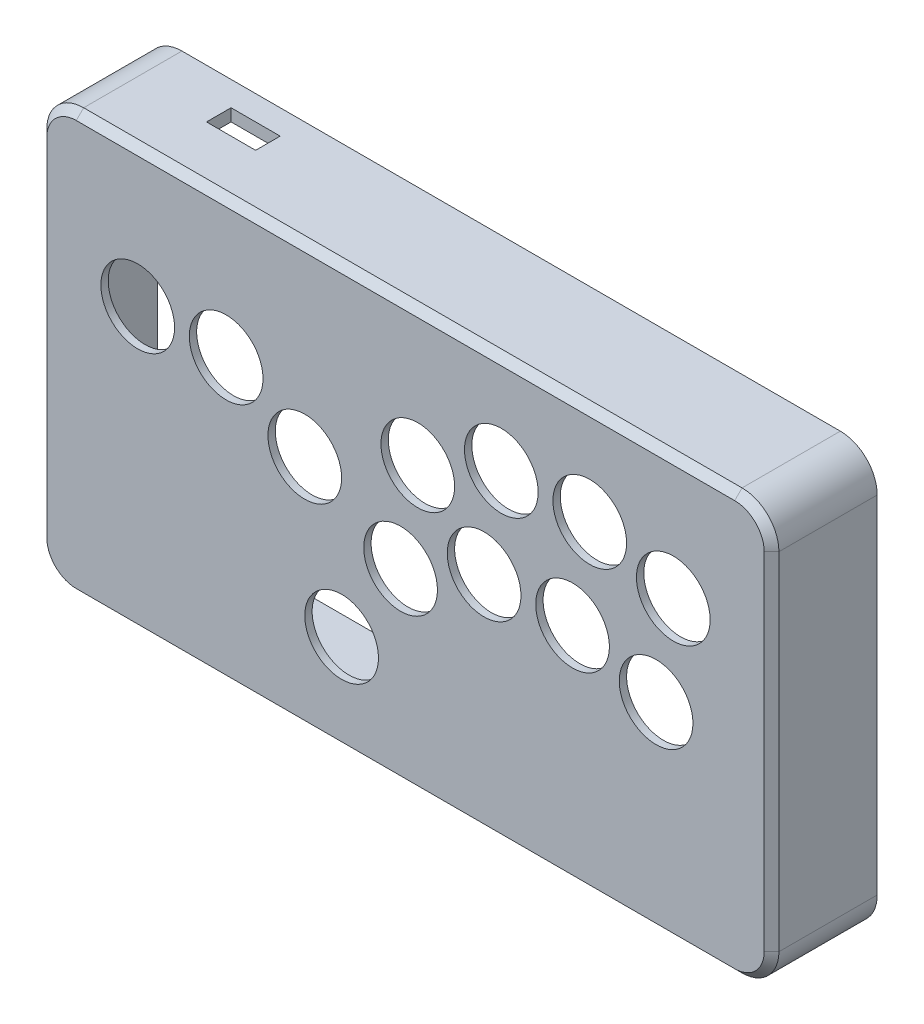
SolidWorks part; units mm, degrees
ref_plane "Front Plane" through (0, 0, 0) normal (0, 0, 1) x (1, 0, 0)
ref_plane "Top Plane" through (0, 0, 0) normal (0, 1, 0) x (1, 0, 0)
ref_plane "Right Plane" through (0, 0, 0) normal (1, 0, 0) x (0, 0, -1)
sketch "Sketch1" plane through (0, 0, 0) normal (0, 0, 1) x (1, 0, 0)
  line L0 (-30, 56) -> (0, 56) construction
  line L1 (-123, 116) -> (-123, -25)
  line L6 (-98, 106) -> (150, 106) construction
  line L7 (-98, 106) -> (-98, -15) construction
  line L8 (-98, -15) -> (150, -15) construction
  line L9 (150, 106) -> (150, -15) construction
  line L10 (-108, -40) -> (160, -40)
  line L11 (175, 116) -> (175, -25)
  line L12 (-108, 131) -> (160, 131)
  line L13 (-123, -40) -> (175, -40) construction
  line L14 (175, 131) -> (175, -40) construction
  line L15 (-123, 131) -> (175, 131) construction
  line L16 (-123, 131) -> (-123, -40) construction
  circle A0 centre (0, 0) radius 15
  circle A1 centre (-47, 75) radius 15
  circle A2 centre (-15, 56) radius 15
  circle A3 centre (-83, 75) radius 15
  circle A4 centre (31, 76) radius 15
  circle A5 centre (65, 91) radius 15
  circle A6 centre (101, 91) radius 15
  circle A7 centre (24, 36) radius 15
  circle A8 centre (58, 51) radius 15
  circle A9 centre (94, 51) radius 15
  circle A10 centre (135, 81) radius 15
  circle A11 centre (128, 41) radius 15
  arc A12 (160, -40) -> (175, -25) centre (160, -25) ccw
  arc A13 (160, 131) -> (175, 116) centre (160, 116) cw
  arc A14 (-123, 116) -> (-108, 131) centre (-108, 116) cw
  arc A15 (-123, -25) -> (-108, -40) centre (-108, -25) ccw
  point P25 (-15, 0)
  point P26 (-15, 0)
  point P27 (-15, 56)
  dimension "D3" = 30
  dimension "D22" = 15
  dimension "D1" = 56
  dimension "D2" = 32
  dimension "D4" = 36
  dimension "D5" = 19
  dimension "D6" = 36
  dimension "D7" = 34
  dimension "D8" = 36
  dimension "D9" = 34
  dimension "D10" = 15
  dimension "D11" = 10
  dimension "D12" = 24
  dimension "D13" = 40
  dimension "D14" = 7
  dimension "D15" = 40
  dimension "D16" = 40
  dimension "D17" = 40
  dimension "D18" = 7
  dimension "D19" = 7
  dimension "D20" = 7
  dimension "D21" = 25
  dimension "D23" = 298
  dimension "D24" = 171
extrude "Boss-Extrude1" add sketch "Sketch1" against normal blind 3
sketch "Sketch2" plane through (0, 0, -3) normal (0, 0, -1) x (-1, 0, 0)
  line L4 (123, -25) -> (123, 116)
  line L5 (108, 131) -> (-160, 131)
  line L6 (-175, 116) -> (-175, -25)
  line L7 (-160, -40) -> (108, -40)
  line L8 (118, -25) -> (118, 116)
  line L9 (-160, -35) -> (108, -35)
  line L10 (-170, 116) -> (-170, -25)
  line L11 (108, 126) -> (-160, 126)
  line L12 (118, -25) -> (118, 116)
  line L13 (-160, -35) -> (108, -35)
  line L14 (-170, 116) -> (-170, -25)
  line L15 (108, 126) -> (-160, 126)
  arc A4 (123, 116) -> (108, 131) centre (108, 116) ccw
  arc A5 (-160, 131) -> (-175, 116) centre (-160, 116) ccw
  arc A6 (-175, -25) -> (-160, -40) centre (-160, -25) ccw
  arc A7 (108, -40) -> (123, -25) centre (108, -25) ccw
  arc A8 (118, 116) -> (108, 126) centre (108, 116) ccw
  arc A12 (108, -35) -> (118, -25) centre (108, -25) ccw
  arc A13 (-170, -25) -> (-160, -35) centre (-160, -25) ccw
  arc A14 (-160, 126) -> (-170, 116) centre (-160, 116) ccw
  arc A15 (118, 116) -> (108, 126) centre (108, 116) ccw
  arc A16 (108, -35) -> (118, -25) centre (108, -25) ccw
  arc A17 (-170, -25) -> (-160, -35) centre (-160, -25) ccw
  arc A18 (-160, 126) -> (-170, 116) centre (-160, 116) ccw
  dimension "D1" = 5
  dimension "D2" = 5
extrude "Boss-Extrude2" add sketch "Sketch2" along normal blind 40
chamfer "Chamfer1" distance 3 angle 45 8 edges at (26, -40, 0) (170.6066, -35.6066, 0) (175, 45.5, 0) (170.6066, 126.6066, 0) (26, 131, 0) (-118.6066, 126.6066, 0) (-123, 45.5, 0) (-118.6066, -35.6066, 0)
sketch "Sketch4" plane through (0, 0, -3) normal (0, 0, -1) x (-1, 0, 0)
  circle A4 centre (-160, 116) radius 10
  circle A16 centre (108, 116) radius 10
  circle A18 centre (-160, -25) radius 10
  circle A19 centre (108, -25) radius 10
  point P2 (0, 0)
  point P5 (0, 0)
  point P10 (-160, 116)
  point P11 (0, 0)
  point P12 (0, 0)
  point P13 (0, 0)
  dimension "D1" = 20
  dimension "D4" = 20
  dimension "D2" = 268
  dimension "D3" = 141
extrude "Boss-Extrude3" add sketch "Sketch4" along normal offset from surface (35 mm away) 5 up to face at (26, 45.5, -43)
sketch "Sketch6" plane through (0, 131, 0) normal (0, 1, 0) x (1, 0, 0)
  line L0 (-108, 43) -> (-108, 3) construction
  line L1 (-78, 33) -> (-58, 33)
  line L2 (-78, 33) -> (-78, 23)
  line L3 (-78, 23) -> (-58, 23)
  line L4 (-58, 33) -> (-58, 23)
  line L5 (-108, 3) -> (160, 3) construction
  dimension "D1" = 10
  dimension "D2" = 20
  dimension "D3" = 30
  dimension "D4" = 20
extrude "Cut-Extrude1" cut sketch "Sketch6" against normal up to surface (5 mm away) up to face at (26, 126, -28)
sketch "Sketch8" plane through (0, 0, -38) normal (0, 0, -1) x (-1, 0, 0)
  circle A0 centre (-160, 116) radius 1.5
  circle A1 centre (108, 116) radius 1.5
  circle A2 centre (-160, -25) radius 1.5
  circle A3 centre (108, -25) radius 1.5
  dimension "D1" = 3
extrude "Cut-Extrude3" cut sketch "Sketch8" against normal blind 4 contours A2 | A3 | A1 | A0
